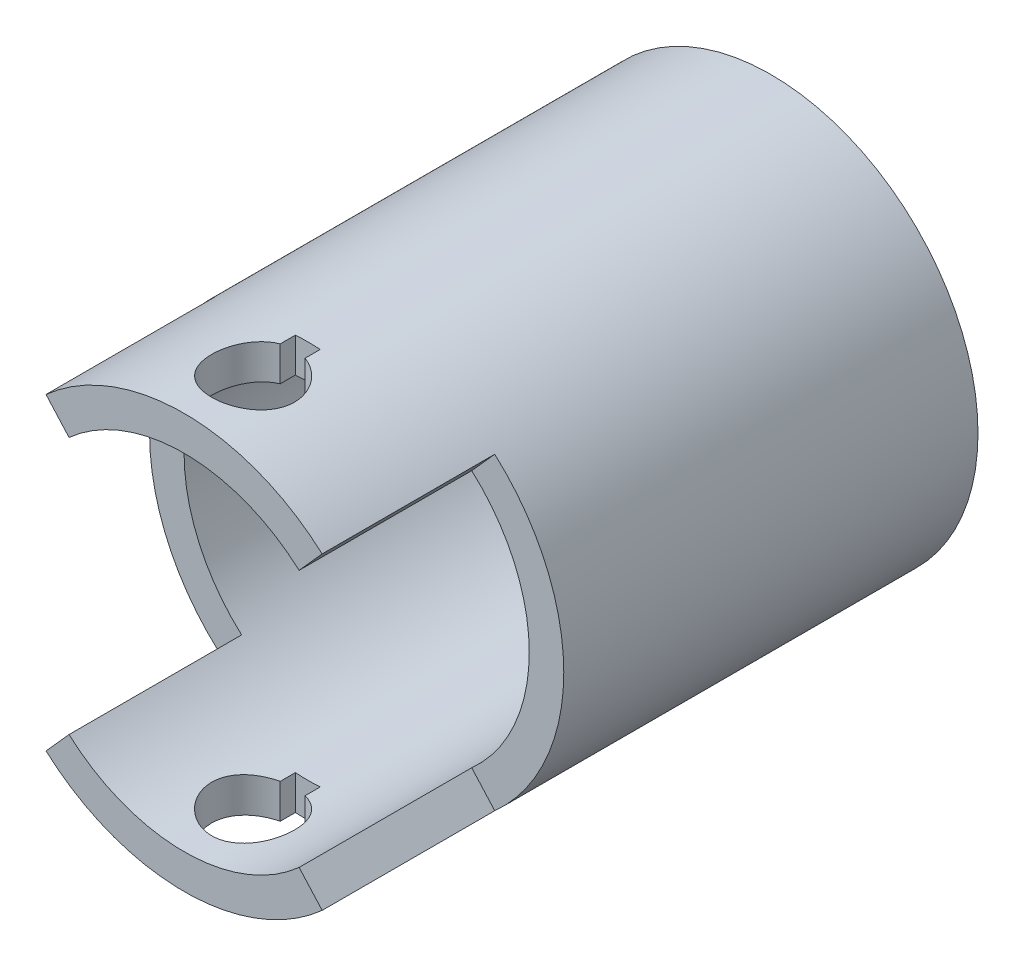
SolidWorks part; units mm, degrees
ref_plane "Front Plane" through (0, 0, 0) normal (1, 0, 0) x (0, 1, 0)
ref_plane "Top Plane" through (0, 0, 0) normal (0, 0, 1) x (0, 1, 0)
ref_plane "Right Plane" through (0, 0, 0) normal (0, 1, 0) x (-1, 0, 0)
sketch "Sketch1" plane through (0, 0, 0) normal (0, 0, 1) x (0, 1, 0)
  circle A0 centre (0, 0) radius 15
  circle A1 centre (0, 0) radius 12.5
  dimension "D1" = 30
  dimension "D2" = 25
extrude "Boss-Extrude1" add sketch "Sketch1" along normal blind 30
sketch "Sketch2" plane through (0, 0, 0) normal (1, 0, 0) x (0, 1, 0)
  line L0 (0, 0) -> (0, 30) construction
  line L1 (15, 30) -> (-15, 30) construction
  line L2 (-15, 15) -> (15, 15) construction
  line L3 (-15, 30) -> (-15, 0) construction
  line L4 (15, 0) -> (15, 30) construction
  line L5 (-6, 30) -> (-6, 0) construction
  line L6 (-15, 0) -> (15, 0) construction
  line L7 (12.5, 30) -> (-12.5, 30) construction
  line L8 (6, 30) -> (6, 0) construction
  line L9 (-15, 30) -> (15, 30) construction
  line L10 (-15, 21) -> (15, 21) construction
  line L11 (-15, 27.5) -> (15, 27.5) construction
  line L12 (-8.5, 30) -> (-8.5, 0) construction
  line L13 (8.5, 30) -> (8.5, 0) construction
  arc A0 (-15, 15) -> (-8.5, 21) centre (-19.3163, 26.1968) ccw
  arc A1 (-6, 27.5) -> (6, 27.5) centre (0, 21.55) cw
  arc A2 (-8.5, 21) -> (-6, 27.5) centre (108.183, -20.1473) cw
  arc A3 (15, 15) -> (8.5, 21) centre (19.3163, 26.1968) cw
  arc A4 (8.5, 21) -> (6, 27.5) centre (-108.183, -20.1473) ccw
  point P40 (0, 0)
  dimension "D9" = 12
  dimension "D10" = 123.7256
  dimension "D1" = 15
  dimension "D2" = 30
  dimension "D3" = 6
  dimension "D4" = 6
  dimension "D5" = 6
  dimension "D6" = 2.5
  dimension "D7" = 2.5
  dimension "D8" = 2.5
ref_plane "Plane1" through (15, 0, 0) normal (1, 0, 0) x (0, 0, -1)
ref_plane "Plane2" through (0, 0, 30) normal (0, 0, 1) x (1, 0, 0)
sketch "Sketch4" plane through (0, 0, 30) normal (0, 0, 1) x (1, 0, 0)
  line L0 (-10, 11.1803) -> (-10, -11.1803) construction
  line L1 (-10, -11.1803) -> (10, -11.1803) construction
  line L2 (10, -11.1803) -> (10, 11.1803) construction
  line L3 (10, 11.1803) -> (-10, 11.1803) construction
  line L4 (-10, 11.1803) -> (10, -11.1803) construction
  line L5 (-10, -11.1803) -> (10, 11.1803) construction
  line L6 (-10, -11.1803) -> (-8.3333, -9.3169)
  line L7 (10, -11.1803) -> (8.3333, -9.3169)
  line L8 (-10, 0) -> (10, 0) construction
  line L9 (-10, 11.1803) -> (-8.3333, 9.3169)
  line L10 (10, 11.1803) -> (8.3333, 9.3169)
  circle A0 centre (0, 0) radius 15 construction
  arc A1 (-10, -11.1803) -> (10, -11.1803) centre (0, 0) ccw
  arc A2 (-8.3333, -9.3169) -> (8.3333, -9.3169) centre (0, 0) ccw
  circle A3 centre (0, 0) radius 12.5 construction
  arc A4 (-10, 11.1803) -> (10, 11.1803) centre (0, 0) cw
  arc A5 (-8.3333, 9.3169) -> (8.3333, 9.3169) centre (0, 0) cw
  dimension "D1" = 20
extrude "Boss-Extrude2" add sketch "Sketch4" along normal blind 12.5
ref_plane "Plane4" through (0, 15, 0) normal (0, 1, 0) x (1, 0, 0)
sketch "Sketch5" plane through (0, 15, 0) normal (0, 1, 0) x (1, 0, 0)
  line L0 (-10, -42.5) -> (-10, -30) construction
  line L1 (-10, -30) -> (-10, -42.5)
  line L2 (-10, -42.5) -> (10, -42.5)
  line L3 (-10, -37) -> (10, -37) construction
  line L4 (-10, -42.5) -> (-10, -30) construction
  line L5 (10, -42.5) -> (10, -30) construction
  line L6 (0, 0) -> (0, -42.5) construction
  line L7 (-10, -42.5) -> (10, -42.5) construction
  line L8 (10, -42.5) -> (10, -30)
  arc A0 (-6.325, -37) -> (6.3749, -37) centre (0.0249, -36.0844) ccw
  spline S0 degree 2 poles (-10, -30) (-7.0628, -34.406) (-5.4672, -39.4005) knots 0 0 0 1 1 1
  spline S1 degree 2 poles (10, -30) (7.0628, -34.406) (5.4672, -39.4005) knots 0 0 0 1 1 1
  dimension "D3" = 6.4156
  dimension "D4" = 10.4704
  dimension "D1" = 20
  dimension "D2" = 5.5
  dimension "D5" = 3.675
fillet "Fillet1" [suppressed] radius 15
fillet "Fillet2" [suppressed] radius 5
fillet "Fillet3" [suppressed] radius 15
fillet "Fillet4" [suppressed] radius 5
fillet "Fillet5" [suppressed] radius 2
sketch "Sketch6" plane through (0, 15, 0) normal (0, 1, 0) x (1, 0, 0)
  line L0 (-10, -42.5) -> (10, -42.5) construction
  line L1 (10, -42.5) -> (10, -30) construction
  line L2 (-0.9, -34.6382) -> (-0.9, -33.5382)
  line L5 (-0.9, -33.5382) -> (0.9, -33.5382)
  line L11 (0.9, -34.6382) -> (0.9, -33.5382)
  arc A0 (-0.9, -34.6382) -> (0.9, -34.6382) centre (0, -37.5) ccw
  dimension "D1" = 6
  dimension "D2" = 5
  dimension "D3" = 10
  dimension "D4" = 1.8
  dimension "D5" = 1.1
  dimension "D6" = 1.1
  dimension "D7" = 3.9618
  dimension "D8" = 0.9
extrude "Cut-Extrude1" cut sketch "Sketch6" against normal blind 35
